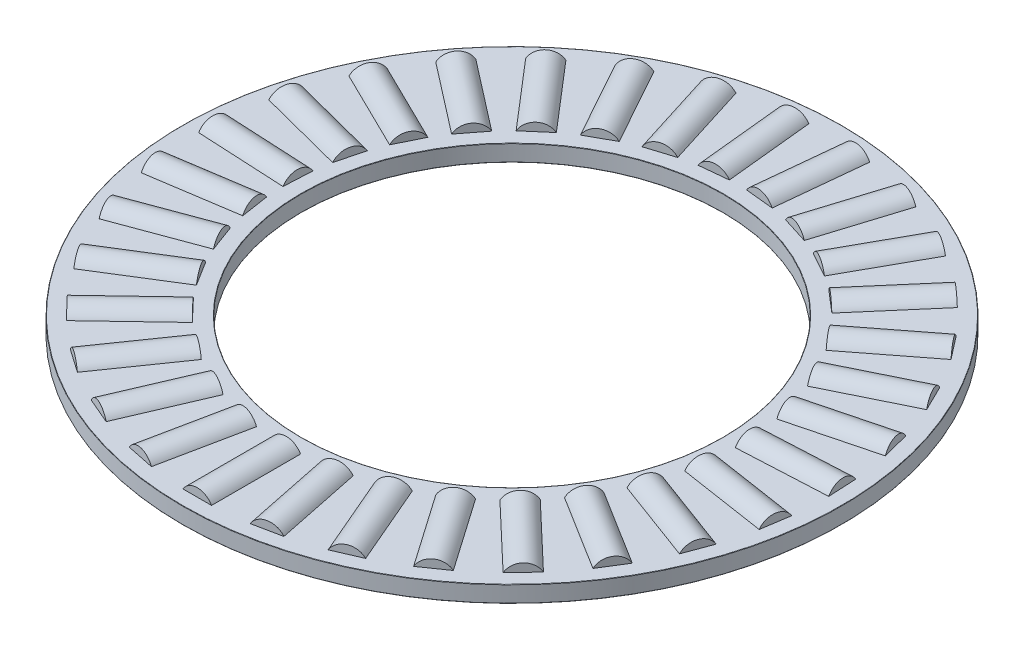
SolidWorks part; units mm, degrees
ref_plane "Front Plane" through (0, 0, 0) normal (0, 0, 1) x (1, 0, 0)
ref_plane "Top Plane" through (0, 0, 0) normal (0, 1, 0) x (1, 0, 0)
ref_plane "Right Plane" through (0, 0, 0) normal (1, 0, 0) x (0, 0, -1)
sketch "Sketch1" plane through (0, 0, 0) normal (1, 0, 0) x (0, 0, -1)
  line L0 (-19.8438, 0) -> (19.8438, 0) construction
  line L1 (0, -0.9922) -> (0, 0.9922) construction
  line L2 (-19.8438, 0.4961) -> (-12.7, 0.4961)
  line L3 (-19.8438, 0.4961) -> (-19.8438, -0.4961)
  line L4 (-19.8438, -0.4961) -> (-12.7, -0.4961)
  line L5 (-12.7, 0.4961) -> (-12.7, -0.4961)
  line L7 (-16.2719, 0.9922) -> (-16.2719, 0.4961) construction
  line L8 (-18.9508, 0.9922) -> (-13.593, 0.9922) construction
  line L9 (-18.9508, 0.9922) -> (-18.9508, -0.9922) construction
  line L10 (-18.9508, -0.9922) -> (-13.593, -0.9922) construction
  line L11 (-13.593, 0.9922) -> (-13.593, -0.9922) construction
  point P16 (-18.9508, 0)
  dimension "OD" = 39.6875
  dimension "Shaft Dia" = 25.4
  dimension "Th" = 1.9844
  dimension "D2" = 0.9922
  dimension "D1" = 5.3578
  dimension "D3" = 7.1438
revolve "Revolve1" add sketch "Sketch1" angle 360 about L1
sketch "Sketch3" plane through (0, 0, 0) normal (1, 0, 0) x (0, 0, -1)
  line L0 (-18.9508, 0.9922) -> (-18.9508, -0.9922) construction
  line L1 (-18.9508, 0) -> (-13.593, 0)
  line L2 (-18.9508, 0) -> (-18.9508, 0.9922)
  line L3 (-18.9508, 0.9922) -> (-13.593, 0.9922)
  line L4 (-13.593, 0) -> (-13.593, 0.9922)
revolve "Cut-Revolve1" cut sketch "Sketch3" angle 360 about L1
sketch "Sketch2" plane through (0, 0, 0) normal (1, 0, 0) x (0, 0, -1)
  line L1 (-18.9508, 0) -> (-13.593, 0)
  line L2 (-18.9508, 0) -> (-18.9508, 0.9922)
  line L3 (-18.9508, 0.9922) -> (-13.593, 0.9922)
  line L4 (-13.593, 0) -> (-13.593, 0.9922)
revolve "Revolve2" add sketch "Sketch2" angle 360 about L1
ref_axis "Axis1" through (0, 0.9922, 0) along (0, -1, 0)
pattern_circular "CirPattern1" count 31 every 11.613 about axis through (0, 0.9922, 0) along (0, -1, 0) of bodies 187 411
pattern_circular "CirPattern2" count 31 every 11.613 about axis through (0, 0, 0) along (0, 1, 0) of "Cut-Revolve1"
sketch "Sketch4" plane through (0, 0, 0) normal (1, 0, 0) x (0, 0, -1)
  line L0 (-19.8438, 0.4961) -> (-19.8438, -0.4961) construction
  line L1 (-19.8438, 9.1091) -> (-12.7, 9.1091)
  line L2 (-19.8438, 9.1091) -> (-19.8438, 9.9219)
  line L3 (-19.8438, 9.9219) -> (-12.7, 9.9219)
  line L4 (-12.7, 9.1091) -> (-12.7, 9.9219)
  line L5 (-19.8438, -9.9219) -> (-12.7, -9.9219)
  line L6 (-19.8438, -9.9219) -> (-19.8438, -9.1091)
  line L7 (-19.8438, -9.1091) -> (-12.7, -9.1091)
  line L8 (-12.7, -9.9219) -> (-12.7, -9.1091)
  line L10 (-12.7, 0.4961) -> (-12.7, -0.4961) construction
  line L11 (0, 0) -> (-19.8438, 0) construction
  line L12 (-19.8438, 0) -> (19.8438, 0) construction
  line L13 (0, -0.9922) -> (0, 0.9922) construction
  dimension "Ht" = 19.8438
  dimension "Washer Th" = 0.8128
  dimension "Washer ID" = 25.4
  dimension "Washer OD" = 39.6875
revolve "Revolve3" [suppressed] add sketch "Sketch4" angle 360 about L1
fillet "Fillet1" [suppressed] radius 0.0198
fillet "Fillet2" radius 0.0198 4 edges at (0, -0.4961, -12.7) (0, 0.4961, -12.7) (0, -0.4961, -19.8438) (0, 0.4961, -19.8438)
fillet "Fillet3" [suppressed] radius 0.0198
equation "\"D2@Sketch1\" = \"Th@Sketch1\"*.5"
equation "\"D1@Fillet1\" = \"Th@Sketch1\"*.01"
equation "\"D1@Fillet2\" = \"D1@Fillet1\""
equation "\"D1@Fillet3\" = \"D1@Fillet1\""
equation "\"D1@Sketch1\" = \"D3@Sketch1\"*.75"
equation "\"Angle@CirPattern1\" = 360/\"Rollers@CirPattern1\""
equation "\"Rollers@CirPattern1\" = \"OD@Sketch1\"*20"
equation "\"D1@CirPattern2\" = \"Rollers@CirPattern1\""
equation "\"D2@CirPattern2\" = \"Angle@CirPattern1\""
equation "\"Ht@Sketch4\" = \"Th@Sketch1\"*10"
